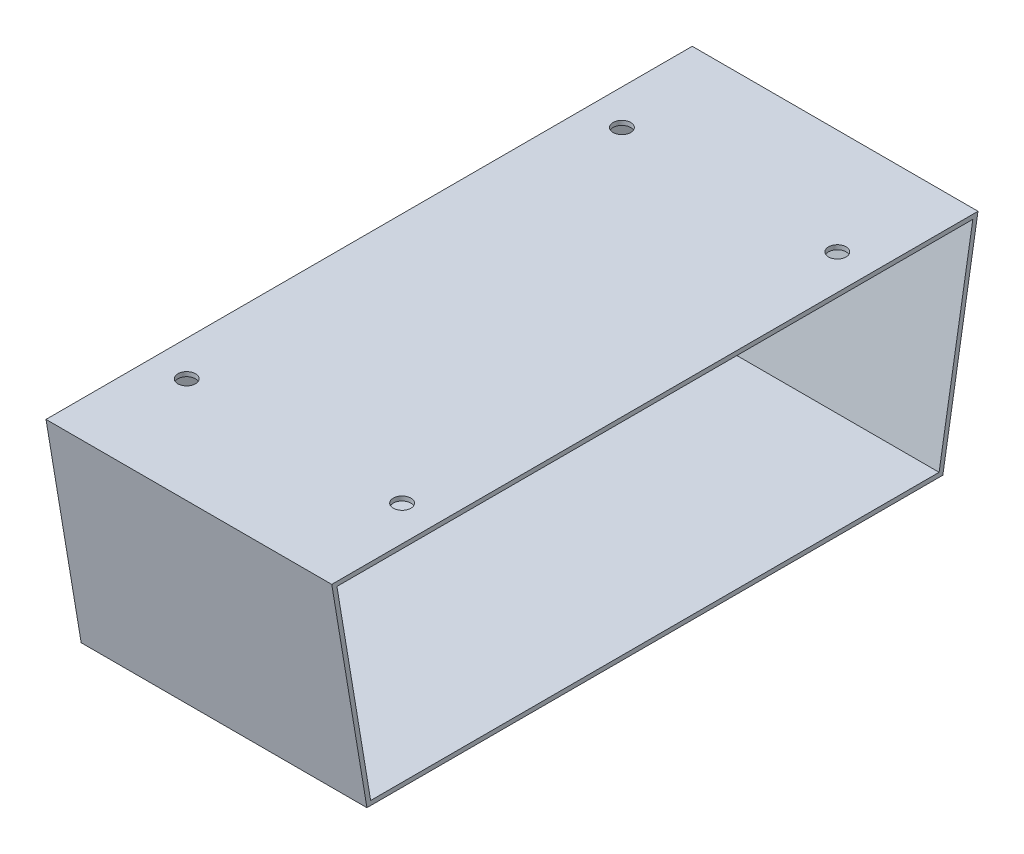
SolidWorks part; units mm, degrees
ref_plane "Front" through (0, 0, 0) normal (0, 0, 1) x (1, 0, 0)
ref_plane "Top" through (0, 0, 0) normal (0, 1, 0) x (1, 0, 0)
ref_plane "Right" through (0, 0, 0) normal (1, 0, 0) x (0, 0, -1)
sketch "Sketch1" plane through (0, 0, 0) normal (1, 0, 0) x (0, 0, -1)
  line L0 (-358.3169, 16.7487) -> (-383.7169, 169.1487)
  line L1 (-383.7169, 169.1487) -> (83.0081, 169.1487)
  line L2 (83.0081, 169.1487) -> (57.6081, 16.7487)
  line L3 (57.6081, 16.7487) -> (-358.3169, 16.7487)
  dimension "D1" = 466.725
  dimension "D2" = 415.925
  dimension "D3" = 152.4
extrude "Boss-Extrude1" add sketch "Sketch1" along normal blind 3.175
sketch "Sketch2" plane through (3.175, 0, 0) normal (1, 0, 0) x (0, 0, -1)
  line L0 (-383.7169, 169.1487) -> (-358.3169, 16.7487)
  line L1 (-358.3169, 16.7487) -> (57.6081, 16.7487)
  line L2 (57.6081, 16.7487) -> (83.0081, 169.1487)
  line L3 (83.0081, 169.1487) -> (-383.7169, 169.1487)
  line L10 (54.9185, 19.9237) -> (79.2602, 165.9737)
  line L11 (-355.6272, 19.9237) -> (54.9185, 19.9237)
  line L12 (-379.9689, 165.9737) -> (-355.6272, 19.9237)
  line L13 (79.2602, 165.9737) -> (-379.9689, 165.9737)
  line L14 (54.9185, 19.9237) -> (79.2602, 165.9737)
  line L15 (-355.6272, 19.9237) -> (54.9185, 19.9237)
  line L16 (-379.9689, 165.9737) -> (-355.6272, 19.9237)
  line L17 (79.2602, 165.9737) -> (-379.9689, 165.9737)
  dimension "D1" = 3.175
  dimension "D2" = 3.175
extrude "Boss-Extrude2" add sketch "Sketch2" along normal blind 203.2
sketch "Sketch3" plane through (0, 169.1487, 0) normal (0, 1, 0) x (1, 0, 0)
  line L9 (206.375, 83.0081) -> (206.375, -383.7169) construction
  line L10 (0, 83.0081) -> (0, -383.7169) construction
  line L11 (206.375, 83.0081) -> (0, 83.0081) construction
  line L12 (206.375, -150.3544) -> (0, -150.3544) construction
  circle A2 centre (180.975, 6.8081) radius 6.35
  circle A3 centre (25.4, 6.8081) radius 6.35
  circle A4 centre (25.4, -307.5169) radius 6.35
  circle A5 centre (180.975, -307.5169) radius 6.35
  dimension "D1" = 12.7
  dimension "D2" = 12.7
  dimension "D3" = 25.4
  dimension "D4" = 25.4
  dimension "D5" = 76.2
  dimension "D6" = 76.2
extrude "Cut-Extrude1" cut sketch "Sketch3" against normal blind 3.175
